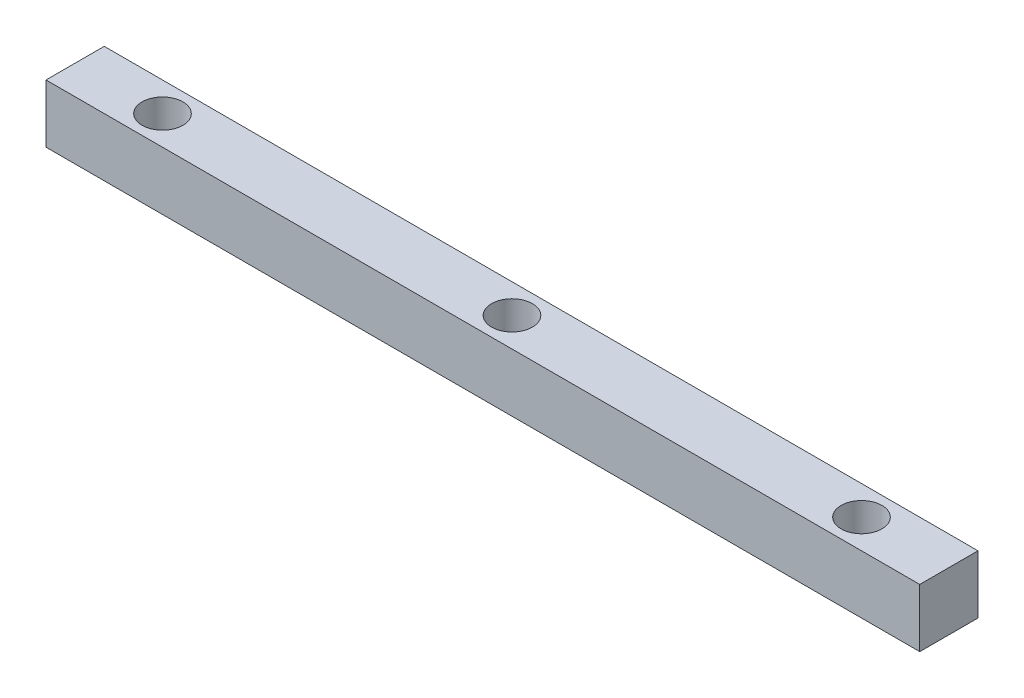
SolidWorks part; units mm, degrees
ref_plane "Front Plane" through (0, 0, 0) normal (0, 0, 1) x (1, 0, 0)
ref_plane "Top Plane" through (0, 0, 0) normal (0, 1, 0) x (1, 0, 0)
ref_plane "Right Plane" through (0, 0, 0) normal (1, 0, 0) x (0, 0, -1)
sketch "Sketch1" plane through (0, 0, 0) normal (0, 1, 0) x (1, 0, 0)
  line L1 (0, 0) -> (150, 0)
  line L2 (0, 0) -> (0, -10)
  line L3 (0, -10) -> (150, -10)
  line L4 (150, 0) -> (150, -10)
  dimension "D1" = 10
  dimension "D2" = 150
extrude "Boss-Extrude1" add sketch "Sketch1" along normal blind 10
sketch "Sketch2" plane through (0, 10, 0) normal (0, 1, 0) x (1, 0, 0)
  line L0 (0, 0) -> (0, -10) construction
  line L1 (150, -10) -> (150, 0) construction
  line L2 (150, 0) -> (0, 0) construction
  circle A0 centre (15, -5) radius 3.5
  circle A1 centre (75, -5) radius 3.5
  circle A2 centre (135, -5) radius 3.5
  dimension "D1" = 7
  dimension "D2" = 7
  dimension "D3" = 7
  dimension "D4" = 15
  dimension "D5" = 75
  dimension "D6" = 15
  dimension "D7" = 5
  dimension "D8" = 5
  dimension "D9" = 5
extrude "Cut-Extrude1" cut sketch "Sketch2" against normal through all
